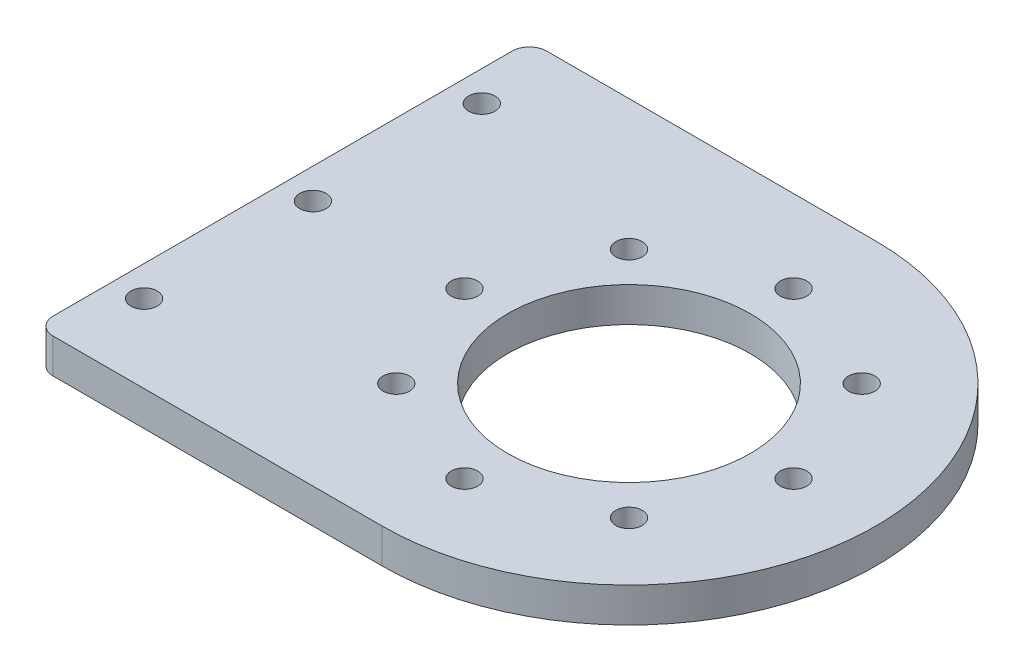
SolidWorks part; units mm, degrees
material "Thornel Mat VMA"
ref_plane "前视基准面" through (0, 0, 0) normal (0, 0, 1) x (1, 0, 0)
ref_plane "上视基准面" through (0, 0, 0) normal (0, 1, 0) x (1, 0, 0)
ref_plane "右视基准面" through (0, 0, 0) normal (1, 0, 0) x (0, 0, -1)
other "Configuration Table"
sketch "草图1" plane through (0, 0, 0) normal (0, 1, 0) x (1, 0, 0)
  line L1 (-19.5, -28.5) -> (19.5, -28.5)
  line L2 (-19.5, -28.5) -> (-19.5, 28.5)
  line L3 (-19.5, 28.5) -> (19.5, 28.5)
  line L4 (19.5, -28.5) -> (19.5, 28.5)
  line L5 (-19.5, -28.5) -> (19.5, 28.5) construction
  line L6 (-19.5, 28.5) -> (19.5, -28.5) construction
  circle A0 centre (19.5, 0) radius 28.5
  point P0 (0, 0)
  dimension "D1" = 57
  dimension "D2" = 39
extrude "凸台-拉伸1" add sketch "草图1" along normal blind 4 contours L4 A0 | A0 L3 L2 L1 | L4 A0
sketch "草图2" plane through (0, 4, 0) normal (0, 1, 0) x (1, 0, 0)
  circle A0 centre (19.5, 0) radius 21.5
  dimension "D1" = 43
sketch "草图3" plane through (0, 4, 0) normal (0, 1, 0) x (1, 0, 0)
  line L0 (32.935, 13.435) -> (19.5, 0) construction
  line L1 (19.5, 0) -> (38.5, 0) construction
  circle A0 centre (19.5, 0) radius 19 construction
  circle A1 centre (32.935, 13.435) radius 1.525
  circle A2 centre (32.935, -13.435) radius 1.525
  circle A3 centre (6.065, -13.435) radius 1.525
  circle A4 centre (6.065, 13.435) radius 1.525
  circle A5 centre (38.5, 0) radius 1.525
  circle A6 centre (19.5, -19) radius 1.525
  circle A7 centre (0.5, 0) radius 1.525
  circle A8 centre (19.5, 19) radius 1.525
  point P15 (19.5, 0)
  point P23 (19.5, 0)
  dimension "D1" = 38
  dimension "D2" = 3.05
  dimension "D5" = 3.05
  dimension "D3" = 45
  dimension "D4" = 4
  dimension "D6" = 4
extrude "切除-拉伸1" cut sketch "草图3" against normal through all
sketch "草图4" plane through (0, 4, 0) normal (0, 1, 0) x (1, 0, 0)
  circle A0 centre (19.5, 0) radius 14
  arc A1 (19.5, -28.5) -> (19.5, 28.5) centre (19.5, 0) ccw construction
  dimension "D1" = 28
extrude "切除-拉伸2" cut sketch "草图4" against normal through all
sketch "草图7" plane through (0, 0, 0) normal (0, -1, 0) x (1, 0, 0)
  circle A0 centre (-17, -19.5) radius 1.8 construction
  circle A1 centre (-17, -19.5) radius 1.25
  circle A2 centre (-17, -19.5) radius 1.25 construction
  circle A3 centre (-17, 0) radius 1.25
  circle A4 centre (-17, 0) radius 1.25 construction
  circle A5 centre (-17, 19.5) radius 1.25
  circle A6 centre (-17, 19.5) radius 1.25 construction
  circle A7 centre (-17, 0) radius 1.8 construction
  circle A8 centre (-17, 19.5) radius 1.8 construction
  circle A23 centre (-17, 0) radius 1.525
  circle A24 centre (-17, 19.5) radius 1.525
  circle A25 centre (-17, -19.5) radius 1.525
  dimension "D4" = 0.55
  dimension "D5" = 3.05
  dimension "D1" = 0
  dimension "D2" = 0
  dimension "D3" = 0
extrude "切除-拉伸4" cut sketch "草图7" against normal through all
sketch "草图8" plane through (0, 4, 0) normal (0, 1, 0) x (1, 0, 0)
  line L0 (-19.5, -28.5) -> (19.5, -28.5) construction
  line L1 (-19.5, 28.5) -> (-20.5, 28.5)
  line L2 (-19.5, 28.5) -> (-19.5, -28.5)
  line L3 (-19.5, -28.5) -> (-20.5, -28.5)
  line L4 (-20.5, 28.5) -> (-20.5, -28.5)
  dimension "D1" = 1
extrude "凸台-拉伸2" add sketch "草图8" against normal up to surface (4 mm away) up to face at (-17, 0, -21.025)
fillet "圆角1" radius 2 2 edges at (-20.5, 2, 28.5) (-20.5, 2, -28.5)
